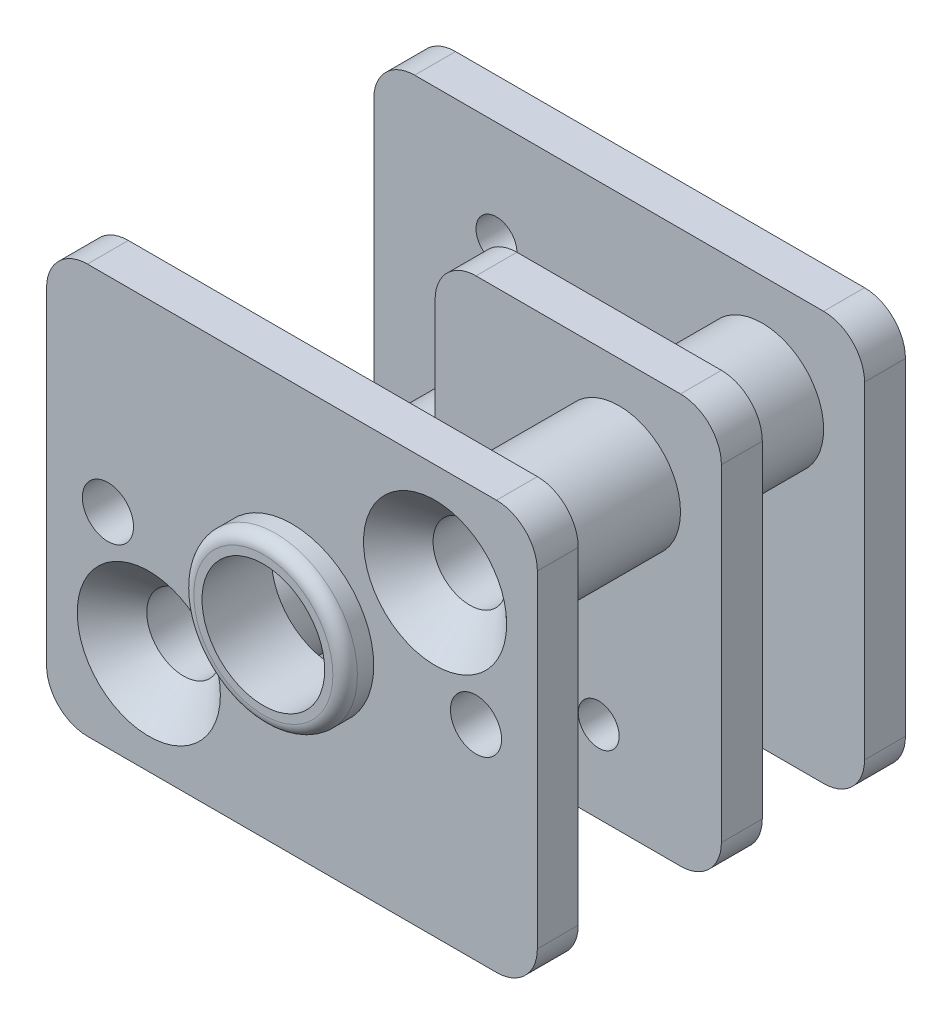
SolidWorks part; units mm, degrees
material "铜"
ref_plane "前视基准面" through (0, 0, 0) normal (0, 0, 1) x (1, 0, 0)
ref_plane "上视基准面" through (0, 0, 0) normal (0, 1, 0) x (1, 0, 0)
ref_plane "右视基准面" through (0, 0, 0) normal (1, 0, 0) x (0, 0, -1)
sketch "草图1" plane through (0, 0, 0) normal (0, 0, 1) x (1, 0, 0)
  line L1 (-6, 5) -> (6, 5)
  line L2 (-6, 5) -> (-6, -5)
  line L3 (-6, -5) -> (6, -5)
  line L4 (6, 5) -> (6, -5)
  line L5 (-6, 5) -> (6, -5) construction
  line L6 (-6, -5) -> (6, 5) construction
  circle A0 centre (0, 0) radius 1.5
  point P0 (0, 0)
  dimension "D1" = 12
  dimension "D2" = 10
extrude "凸台-拉伸1" add sketch "草图1" along normal blind 1
sketch "草图4" plane through (0, 0, 0) normal (0, 0, -1) x (-1, 0, 0)
  line L0 (-6, -5) -> (-6, 5) construction
  line L1 (-6, 5) -> (6, 5) construction
  circle A1 centre (-3.5, 2.5) radius 0.9
  circle A3 centre (3.5, -2.5) radius 0.9
  circle A4 centre (-3.5, 2.5) radius 1.5
  circle A5 centre (3.5, -2.5) radius 1.5
  dimension "D1" = 2.5
  dimension "D2" = 2.5
extrude "凸台-拉伸2" add sketch "草图4" along normal blind 3.5
sketch "草图5" plane through (0, 0, -3.5) normal (0, 0, -1) x (-1, 0, 0)
  line L0 (-6, -5) -> (-6, 5) construction
  line L1 (6, -5) -> (-6, -5) construction
  line L2 (-6, -5) -> (-6, 5)
  line L3 (6, -5) -> (-6, -5)
  line L4 (-6, 5) -> (1, 5)
  line L5 (-6, 5) -> (6, 5) construction
  line L6 (1, 5) -> (1, 0)
  line L7 (1, 0) -> (6, 0)
  line L8 (6, 5) -> (6, -5) construction
  line L9 (6, 0) -> (6, -5)
  circle A0 centre (-3, -3) radius 0.5
  circle A1 centre (0, 0) radius 0.5
  dimension "D3" = 2
  dimension "D1" = 5
  dimension "D2" = 5
  dimension "D4" = 3
extrude "凸台-拉伸3" add sketch "草图5" along normal blind 1
sketch "草图6" plane through (0, 0, -4.5) normal (0, 0, -1) x (-1, 0, 0)
  circle A1 centre (3.5, -2.5) radius 1.5
  circle A2 centre (3.5, -2.5) radius 1.5
  circle A3 centre (-3.5, 2.5) radius 1.5
  circle A4 centre (-3.5, 2.5) radius 1.5
  circle A5 centre (3.5, -2.5) radius 0.9
  circle A6 centre (3.5, -2.5) radius 0.9
  circle A7 centre (-3.5, 2.5) radius 0.9
  circle A8 centre (-3.5, 2.5) radius 0.9
  dimension "D1" = 0
  dimension "D2" = 0
  dimension "D3" = 0
  dimension "D4" = 0
extrude "凸台-拉伸4" add sketch "草图6" along normal blind 2.5
sketch "草图7" plane through (0, 0, -7) normal (0, 0, -1) x (-1, 0, 0)
  line L0 (-6, 5) -> (-6, -5) construction
  line L1 (-6, -5) -> (6, -5) construction
  line L2 (-6, 5) -> (-6, -5)
  line L3 (-6, -5) -> (6, -5)
  line L4 (-6, 5) -> (6, 5) construction
  line L5 (6, 5) -> (6, -5) construction
  line L6 (-6, 5) -> (6, 5)
  line L7 (6, 5) -> (6, -5)
  circle A0 centre (0, 0) radius 0.5329
  circle A1 centre (3, 2.5) radius 0.5
  dimension "D1" = 3
  dimension "D2" = 2.5
extrude "凸台-拉伸5" add sketch "草图7" along normal blind 1
fillet "圆角1" radius 1 14 edges at (-6, 5, -7.5) (-6, -5, -7.5) (-6, -5, -4) (-6, 0, -4) (-1, 0, -4) (-1, 5, -4) (6, -5, -7.5) (6, 5, -7.5) (6, 5, -4) (6, -5, -4) (6, -5, 0.5) (6, 5, 0.5) (-6, -5, 0.5) (-6, 5, 0.5)
hole_wizard "打孔尺寸根据开槽半沉头木螺钉的类型1" positions "草图9" profile "草图8" countersink size "M1.6" standard "Gb" end condition up to next
sketch "草图9" plane through (0, 0, 1) normal (0, 0, 1) x (1, 0, 0)
  circle A2 centre (3.5, 2.5) radius 0.9
  circle A3 centre (3.5, 2.5) radius 0.9 construction
  circle A6 centre (-3.5, -2.5) radius 0.9
  circle A7 centre (-3.5, -2.5) radius 0.9 construction
  circle A10 centre (3.5, 2.5) radius 1.5
  circle A11 centre (3.5, 2.5) radius 1.5 construction
  circle A14 centre (-3.5, -2.5) radius 1.5
  circle A15 centre (-3.5, -2.5) radius 1.5 construction
  point P0 (3.5, 2.5)
  point P2 (-3.5, -2.5)
  dimension "D1" = 0
  dimension "D2" = 0
  dimension "D3" = 0
  dimension "D4" = 0
sketch "草图8" plane through (3.5, 2.5, 1) normal (1, 0, 0) x (0, -1, 0)
  line L0 (0, 0) -> (0, 1)
  line L1 (0, 1) -> (0.9, 1)
  line L2 (0.9, 1) -> (0.9, 0.85)
  line L3 (0.9, 0.85) -> (1.75, 0)
  line L5 (1.75, 0) -> (0, 0)
  line L6 (-0.9, 0.85) -> (-1.75, 0) construction
  line L11 (0, -6.35) -> (0, 107.95) construction
  dimension "通孔孔直径" = 1.8
  dimension "通孔孔深度" = 1
  dimension "近端锥形沉头孔直径" = 3.5
  dimension "近端锥形沉头孔角度" = 90
hole_wizard "M1.6 螺纹孔1" positions "草图11" profile "草图10" tap size "M1.6" standard "Gb" end condition up to next
sketch "草图11" plane through (0, 0, 1) normal (0, 0, 1) x (1, 0, 0)
  point P2 (4.5, 0)
  point P4 (-4.5, 0)
  dimension "D1" = 4.5
  dimension "D2" = 4.5
cosmetic thread "孔螺蚊线1" parameters "D2"=1.6
cosmetic thread "孔螺蚊线2" parameters "D2"=1.6
sketch "草图10" plane through (4.5, 0, 1) normal (1, 0, 0) x (0, -1, 0)
  line L0 (0, 0) -> (0, 1)
  line L1 (0, 1) -> (0.625, 1)
  line L2 (0.625, 1) -> (0.625, 0)
  line L5 (0.625, 0) -> (0, 0)
  line L11 (0, -6.35) -> (0, 107.95) construction
  dimension "通孔螺纹孔钻头直径" = 1.25
  dimension "通孔螺纹孔钻头深度" = 1
sketch "草图12" plane through (0, 0, 1) normal (0, 0, 1) x (1, 0, 0)
  circle A0 centre (0, 0) radius 2
  circle A1 centre (0, 0) radius 1.5 construction
  circle A2 centre (0, 0) radius 1.5
extrude "凸台-拉伸6" add sketch "草图12" along normal blind 0.7
fillet "圆角2" radius 0.3 1 edges at (2, 0, 1.7)
